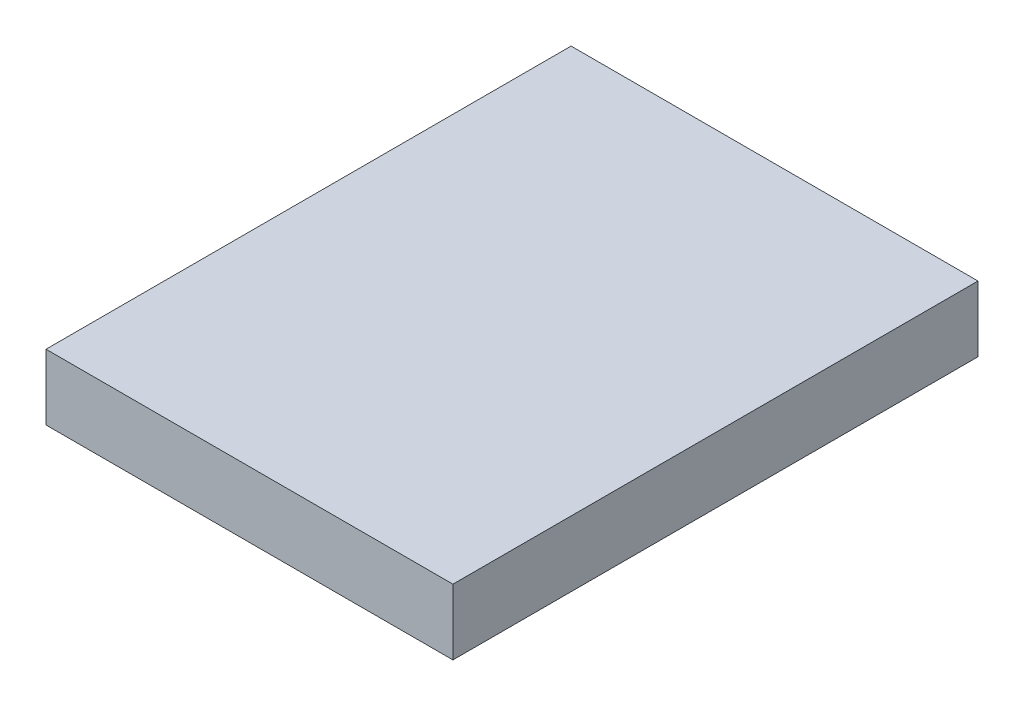
SolidWorks part; units mm, degrees
ref_plane "Alzado" through (0, 0, 0) normal (0, 0, 1) x (1, 0, 0)
ref_plane "Planta" through (0, 0, 0) normal (0, 1, 0) x (1, 0, 0)
ref_plane "Vista lateral" through (0, 0, 0) normal (1, 0, 0) x (0, 0, -1)
sketch "Croquis1" plane through (0, 0, 0) normal (0, 1, 0) x (1, 0, 0)
  line L1 (-15.5, -20) -> (15.5, -20)
  line L2 (-15.5, -20) -> (-15.5, 20)
  line L3 (-15.5, 20) -> (15.5, 20)
  line L4 (15.5, -20) -> (15.5, 20)
  line L5 (-15.5, -20) -> (15.5, 20) construction
  line L6 (-15.5, 20) -> (15.5, -20) construction
  point P0 (0, 0)
  dimension "D1" = 31
  dimension "D2" = 40
extrude "Saliente-Extruir1" add sketch "Croquis1" along normal blind 5
